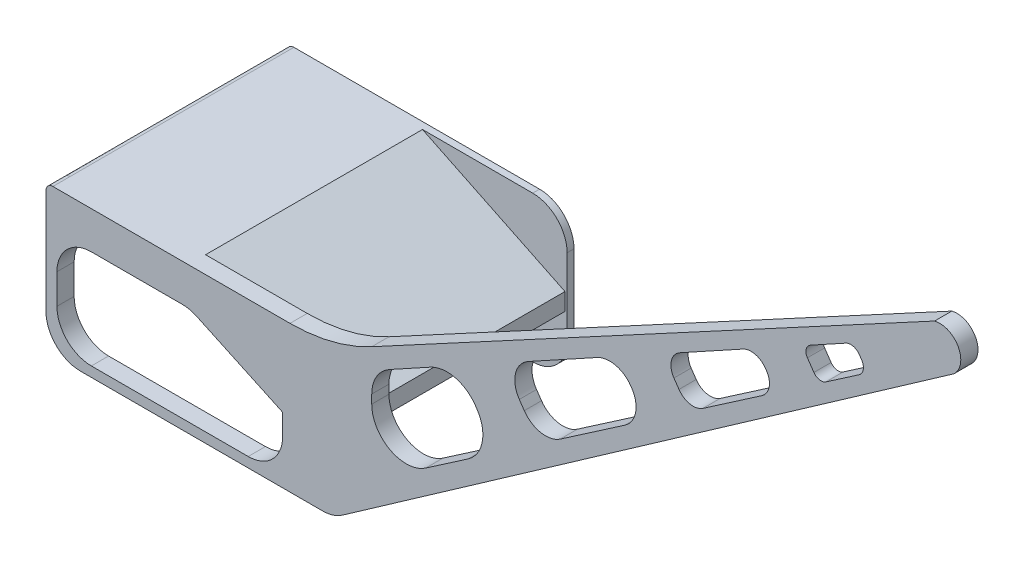
SolidWorks part; units mm, degrees
ref_plane "Front Plane" through (0, 0, 0) normal (0, 0, 1) x (1, 0, 0)
ref_plane "Top Plane" through (0, 0, 0) normal (0, 1, 0) x (1, 0, 0)
ref_plane "Right Plane" through (0, 0, 0) normal (1, 0, 0) x (0, 0, -1)
sketch "Sketch1" plane through (0, 0, 0) normal (0, 0, 1) x (1, 0, 0)
  line L0 (141.2711, -12.5513) -> (182.6177, -12.5513)
  line L2 (182.6177, -12.5513) -> (224, -32.6115)
  line L4 (224, -32.6115) -> (224, -27.6115)
  line L5 (224, -27.6115) -> (182.6177, -7.5513)
  line L7 (182.6177, -7.5513) -> (141.2711, -7.5513)
  line L8 (141.2711, -7.5513) -> (141.2711, -12.5513)
extrude "Boss-Extrude1" add sketch "Sketch1" along normal blind 65
sketch "Sketch2" plane through (0, 0, 65) normal (0, 0, 1) x (1, 0, 0)
  line L4 (144.4463, -28.4108) -> (144.4463, -37.1086)
  line L13 (141.2711, -17.5513) -> (141.2711, -40)
  line L14 (151.2711, -7.5513) -> (212.1344, -7.5513)
  line L15 (151.2711, -50) -> (221.6092, -50)
  line L17 (151.2711, -7.5513) -> (143.2711, -7.5513)
  line L18 (154.4463, -47.1086) -> (200, -47.1086)
  line L19 (227.345, -48.1915) -> (241.1453, -38.5285)
  line L20 (241.1453, -38.5285) -> (404.9757, 76.1868)
  line L21 (235.8757, -1.5553) -> (399.3377, 86.6366)
  line L22 (182.6177, -7.5513) -> (141.2711, -7.5513) construction
  line L23 (210, -37.1086) -> (210, -30.9785)
  line L24 (210, -30.9785) -> (185.0252, -19.3458)
  line L25 (141.2711, -9.5513) -> (141.2711, -17.5513)
  line L26 (180.803, -18.4108) -> (154.4463, -18.4108)
  line L27 (235.8757, -13.4638) -> (235.8757, -16.0035) construction
  line L29 (251.5352, -24.2479) -> (263.8166, -15.8172)
  line L30 (378.1477, 66.3051) -> (377.4926, 67.2594)
  line L31 (252.9068, 1.8167) -> (241.0561, -4.7018)
  line L32 (235.8757, -13.4638) -> (235.8757, -16.0035)
  line L37 (266.4016, -1.9133) -> (265.9708, -1.2858)
  line L40 (280.1831, 4.5148) -> (278.7369, 6.6216)
  line L42 (311.3296, 25.8955) -> (311.1599, 26.1429)
  line L43 (325.1112, 32.3236) -> (323.6457, 34.4584)
  line L45 (350.5043, 49.7549) -> (350.2044, 50.1917)
  line L48 (364.2858, 56.183) -> (362.4101, 58.9153)
  line L49 (281.3055, 17.4376) -> (301.3619, 28.4698)
  line L50 (309.3909, 15.4676) -> (290.611, 2.576)
  line L51 (325.3582, 41.6691) -> (343.6724, 51.7429)
  line L53 (332.0631, 31.0311) -> (349.2118, 42.803)
  line L54 (363.2663, 62.5207) -> (373.5734, 68.1902)
  line L55 (367.7617, 55.5367) -> (377.3723, 62.1339)
  arc A6 (185.0252, -19.3458) -> (180.803, -18.4108) centre (180.803, -28.4108) ccw
  arc A9 (235.8757, -1.5553) -> (212.1344, -7.5513) centre (212.1344, 42.4487) cw
  arc A10 (200, -47.1086) -> (210, -37.1086) centre (200, -37.1086) ccw
  arc A11 (154.4463, -47.1086) -> (144.4463, -37.1086) centre (154.4463, -37.1086) cw
  arc A12 (144.4463, -28.4108) -> (154.4463, -18.4108) centre (154.4463, -28.4108) cw
  arc A13 (227.345, -48.1915) -> (221.6092, -50) centre (221.6092, -40) cw
  arc A15 (151.2711, -50) -> (141.2711, -40) centre (151.2711, -40) cw
  arc A17 (251.5352, -24.2479) -> (235.8757, -16.0035) centre (245.8757, -16.0035) cw
  arc A18 (235.8757, -13.4638) -> (241.0561, -4.7018) centre (245.8757, -13.4638) cw
  arc A19 (377.3723, 62.1339) -> (378.1477, 66.3051) centre (375.6744, 64.6073) ccw
  arc A20 (377.4926, 67.2594) -> (373.5734, 68.1902) centre (375.0193, 65.5616) ccw
  arc A22 (143.2711, -7.5513) -> (141.2711, -9.5513) centre (143.2711, -9.5513) ccw
  arc A23 (265.9708, -1.2858) -> (252.9068, 1.8167) centre (257.7264, -6.9452) ccw
  arc A24 (263.8166, -15.8172) -> (266.4016, -1.9133) centre (258.1572, -7.5728) ccw
  arc A25 (311.3296, 25.8955) -> (309.3909, 15.4676) centre (305.1463, 21.6509) cw
  arc A26 (311.1599, 26.1429) -> (301.3619, 28.4698) centre (304.9765, 21.8983) ccw
  arc A27 (290.611, 2.576) -> (280.1831, 4.5148) centre (286.3664, 8.7593) cw
  arc A28 (281.3055, 17.4376) -> (278.7369, 6.6216) centre (284.9202, 10.8662) ccw
  arc A29 (350.5043, 49.7549) -> (349.2118, 42.803) centre (346.382, 46.9252) cw
  arc A30 (350.2044, 50.1917) -> (343.6724, 51.7429) centre (346.0822, 47.362) ccw
  arc A31 (332.0631, 31.0311) -> (325.1112, 32.3236) centre (329.2334, 35.1533) cw
  arc A32 (323.6457, 34.4584) -> (325.3582, 41.6691) centre (327.768, 37.2881) cw
  arc A33 (362.4101, 58.9153) -> (363.2663, 62.5207) centre (364.4712, 60.3302) cw
  arc A34 (364.2858, 56.183) -> (367.7617, 55.5367) centre (366.3469, 57.5978) ccw
  arc A36 (404.9757, 76.1868) -> (399.3377, 86.6366) centre (400.8269, 80.6942) ccw
  point P50 (141.2711, -7.5513)
  point P68 (315.5742, 19.7122)
  point P76 (274.0512, 13.4474)
  point P79 (353.334, 45.6327)
  point P82 (347.641, 53.9259)
  point P85 (327.9409, 28.2014)
  point P88 (320.522, 39.0089)
  point P91 (360.8482, 61.1906)
  dimension "D1" = 10
  dimension "D2" = 10
  dimension "D3" = 2
  dimension "D4" = 10
  dimension "D5" = 3
  dimension "D7" = 10
  dimension "D8" = 10
  dimension "D9" = 7.5
  dimension "D10" = 5
  dimension "D11" = 2.5
extrude "Boss-Extrude2" add sketch "Sketch2" along normal blind 5
fillet "Fillet1" radius 2 1 edges at (141.2711, -7.5513, 32.5)
sketch "Sketch3" plane through (0, 0, 0) normal (0, 0, -1) x (-1, 0, 0)
  line L1 (-141.2711, -26.2757) -> (-141.2711, -40.0122)
  line L2 (-224.6163, -26.2757) -> (-224.6163, -40.0122)
  line L3 (-151.2711, -50.0122) -> (-214.6163, -50.0122)
  line L4 (-141.2711, -12.5513) -> (-141.2711, -40) construction
  line L5 (-141.2711, -26.2757) -> (-141.2711, -17.5513)
  line L7 (-151.2711, -7.5513) -> (-214.6163, -7.5513)
  line L8 (-224.6163, -26.2757) -> (-224.6163, -17.5513)
  arc A0 (-224.6163, -17.5513) -> (-214.6163, -7.5513) centre (-214.6163, -17.5513) cw
  arc A1 (-214.6163, -50.0122) -> (-224.6163, -40.0122) centre (-214.6163, -40.0122) cw
  arc A2 (-151.2711, -50.0122) -> (-141.2711, -40.0122) centre (-151.2711, -40.0122) ccw
  arc A3 (-141.2711, -17.5513) -> (-151.2711, -7.5513) centre (-151.2711, -17.5513) ccw
  dimension "D1" = 10
extrude "Boss-Extrude3" add sketch "Sketch3" against normal blind 2
